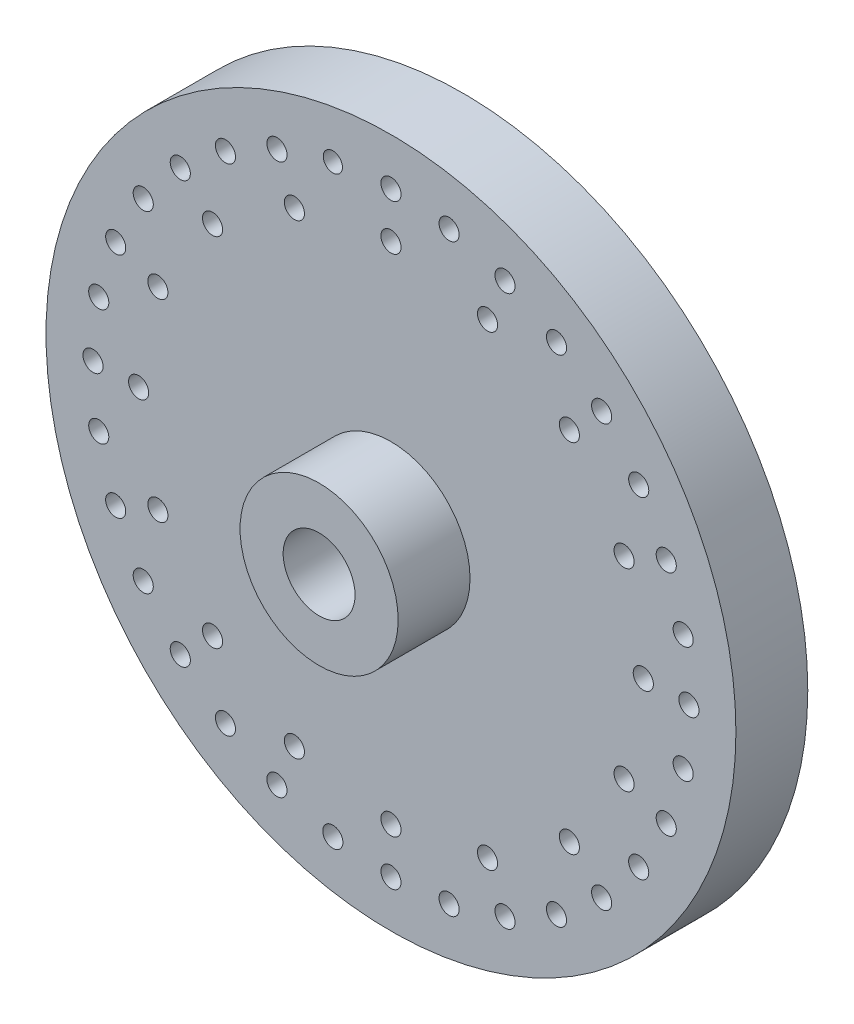
SolidWorks part; units mm, degrees
ref_plane "Front" through (0, 0, 0) normal (0, 0, 1) x (1, 0, 0)
ref_plane "Top" through (0, 0, 0) normal (0, 1, 0) x (1, 0, 0)
ref_plane "Right" through (0, 0, 0) normal (1, 0, 0) x (0, 0, -1)
sketch "Sketch1" plane through (0, 0, 0) normal (0, 0, 1) x (1, 0, 0)
  circle A0 centre (0, 0) radius 24
extrude "Extrude1" add sketch "Sketch1" along normal blind 5
sketch "Sketch2" plane through (0, 0, 5) normal (0, 0, 1) x (1, 0, 0)
  circle A0 centre (0, 0) radius 5.5
extrude "Extrude2" add sketch "Sketch2" along normal blind 5
sketch "Sketch3" plane through (0, 0, 10) normal (0, 0, 1) x (1, 0, 0)
  circle A0 centre (0, 0) radius 2.5
extrude "Cut-Extrude1" cut sketch "Sketch3" against normal through all
sketch "Sketch4" plane through (0, 0, 5) normal (0, 0, 1) x (1, 0, 0)
  circle A0 centre (0, 20.73) radius 0.7
  circle A1 centre (0, -20.73) radius 0.7
  circle A2 centre (20.73, 0) radius 0.7
  circle A3 centre (-20.73, 0) radius 0.7
  circle A4 centre (-14.658, 14.658) radius 0.7
  circle A5 centre (14.658, 14.658) radius 0.7
  circle A6 centre (14.658, -14.658) radius 0.7
  circle A7 centre (-14.658, -14.658) radius 0.7
  circle A8 centre (19.152, 7.933) radius 0.7
  circle A9 centre (7.933, 19.152) radius 0.7
  circle A10 centre (19.152, -7.933) radius 0.7
  circle A11 centre (7.933, -19.152) radius 0.7
  circle A12 centre (-7.933, 19.152) radius 0.7
  circle A13 centre (-19.152, 7.933) radius 0.7
  circle A14 centre (-19.152, -7.933) radius 0.7
  circle A15 centre (-7.933, -19.152) radius 0.7
  circle A16 centre (20.331, 4.044) radius 0.7
  circle A17 centre (20.331, -4.044) radius 0.7
  circle A18 centre (4.044, -20.331) radius 0.7
  circle A19 centre (-4.044, -20.331) radius 0.7
  circle A20 centre (4.044, 20.331) radius 0.7
  circle A21 centre (-4.044, 20.331) radius 0.6677
  circle A22 centre (-20.331, 4.044) radius 0.7
  circle A23 centre (-20.331, -4.044) radius 0.7
  circle A24 centre (17.236, 11.516) radius 0.7
  circle A25 centre (11.516, 17.236) radius 0.7
  circle A26 centre (17.236, -11.516) radius 0.7
  circle A27 centre (11.516, -17.236) radius 0.7
  circle A28 centre (-11.516, -17.236) radius 0.7
  circle A29 centre (-17.236, -11.516) radius 0.7
  circle A30 centre (-17.236, 11.516) radius 0.7
  circle A31 centre (-11.516, 17.236) radius 0.7
  circle A32 centre (0, 17.555) radius 0.7
  circle A33 centre (17.555, 0) radius 0.7
  circle A34 centre (0, -17.555) radius 0.7
  circle A35 centre (-17.555, 0) radius 0.7
  circle A36 centre (-12.413, 12.413) radius 0.7
  circle A37 centre (12.413, 12.413) radius 0.7
  circle A38 centre (12.413, -12.413) radius 0.7
  circle A39 centre (-12.413, -12.413) radius 0.7
  circle A40 centre (-16.218, 6.718) radius 0.7
  circle A41 centre (16.218, 6.718) radius 0.7
  circle A42 centre (16.218, -6.718) radius 0.7
  circle A43 centre (-16.218, -6.718) radius 0.7
  circle A44 centre (6.718, 16.218) radius 0.7
  circle A45 centre (6.718, -16.218) radius 0.7
  circle A46 centre (-6.718, -16.218) radius 0.7
  circle A47 centre (-6.718, 16.218) radius 0.7
extrude "Cut-Extrude2" cut sketch "Sketch4" against normal through all
